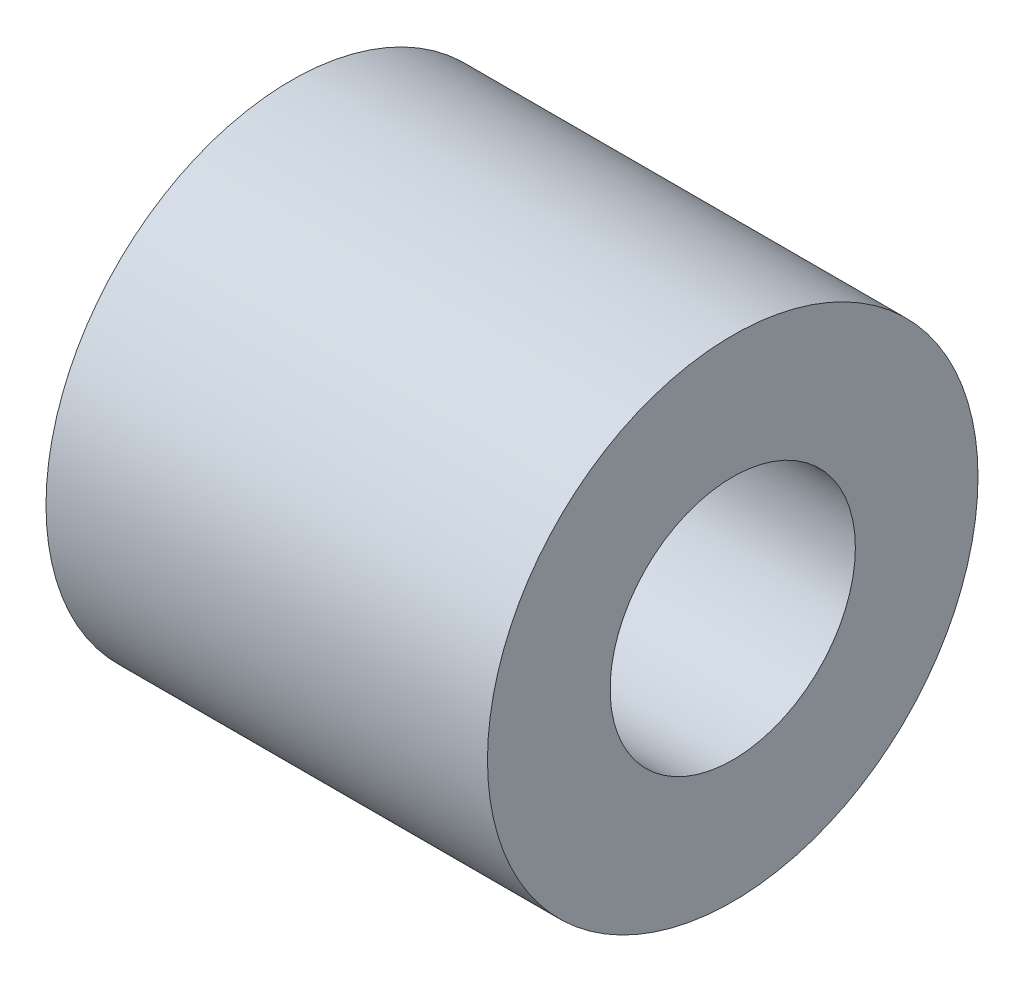
SolidWorks part; units mm, degrees
material "6063-T6"
ref_plane "Front Plane" through (0, 0, 0) normal (0, 0, 1) x (1, 0, 0)
ref_plane "Top Plane" through (0, 0, 0) normal (0, 1, 0) x (1, 0, 0)
ref_plane "Right Plane" through (0, 0, 0) normal (1, 0, 0) x (0, 0, -1)
sketch "Sketch1" plane through (0, 0, 0) normal (1, 0, 0) x (0, 0, -1)
  circle A0 centre (0, 0) radius 2.5
  circle A1 centre (0, 0) radius 5
  dimension "D1" = 5
  dimension "D2" = 10
extrude "Boss-Extrude1" add sketch "Sketch1" along normal blind 9
